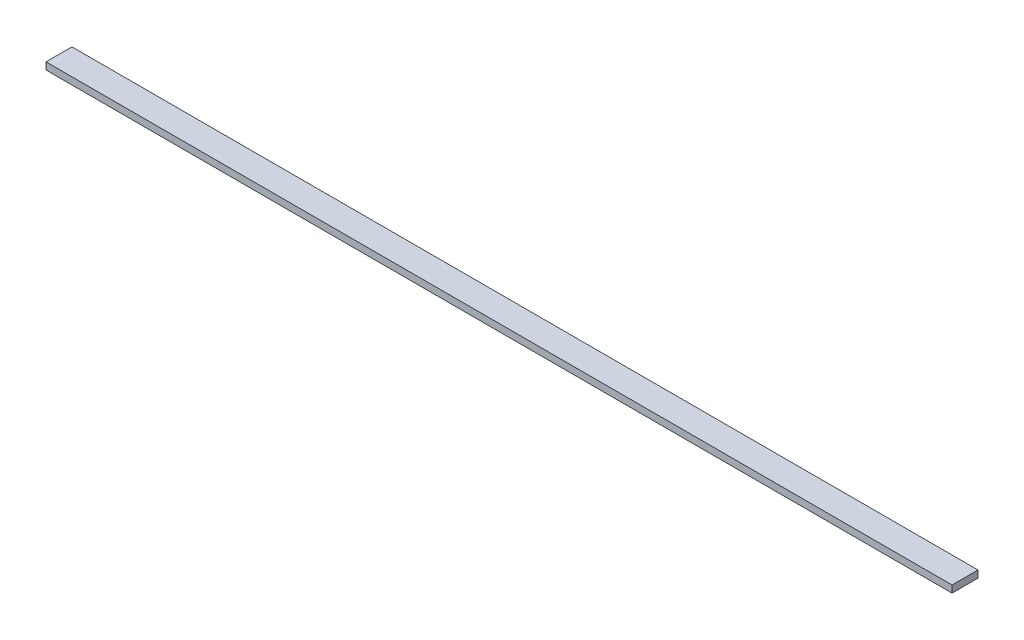
SolidWorks part; units mm, degrees
ref_plane "Front Plane" through (0, 0, 0) normal (0, 0, 1) x (1, 0, 0)
ref_plane "Top Plane" through (0, 0, 0) normal (0, 1, 0) x (1, 0, 0)
ref_plane "Right Plane" through (0, 0, 0) normal (1, 0, 0) x (0, 0, -1)
sketch "Sketch1" plane through (0, 0, 0) normal (0, 1, 0) x (1, 0, 0)
  line L1 (-95.0204, 139.7) -> (4781.7796, 139.7)
  line L2 (-95.0204, 139.7) -> (-95.0204, 0)
  line L3 (-95.0204, 0) -> (4781.7796, 0)
  line L4 (4781.7796, 139.7) -> (4781.7796, 0)
  dimension "D1" = 139.7
  dimension "D2" = 4876.8
extrude "Boss-Extrude1" add sketch "Sketch1" along normal blind 38.1
